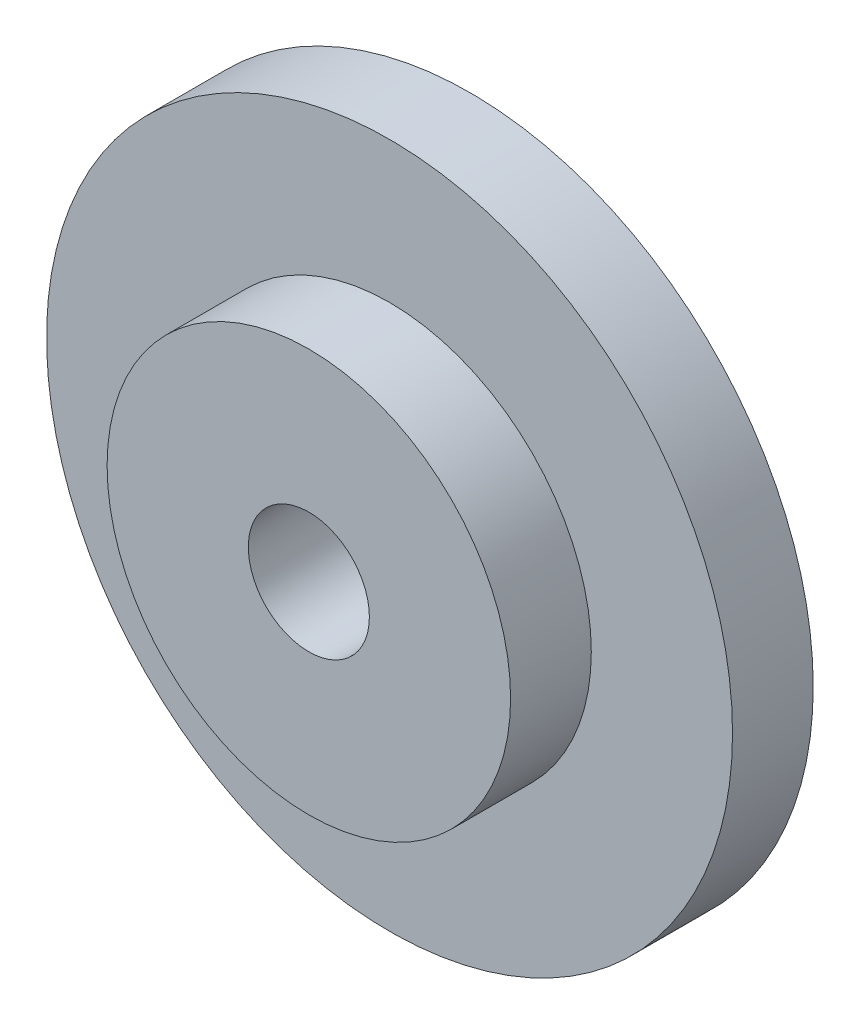
SolidWorks part; units mm, degrees
ref_plane "Front Plane" through (0, 0, 0) normal (0, 0, 1) x (1, 0, 0)
ref_plane "Top Plane" through (0, 0, 0) normal (0, 1, 0) x (1, 0, 0)
ref_plane "Right Plane" through (0, 0, 0) normal (1, 0, 0) x (0, 0, -1)
sketch "Sketch1" plane through (0, 0, 0) normal (0, 0, 1) x (1, 0, 0)
  circle A0 centre (0, 0) radius 8.5
  dimension "D1" = 17
extrude "Boss-Extrude1" add sketch "Sketch1" along normal blind 2
sketch "Sketch2" plane through (0, 0, 2) normal (0, 0, 1) x (1, 0, 0)
  circle A0 centre (0, 0) radius 5
  dimension "D1" = 10
extrude "Boss-Extrude2" add sketch "Sketch2" along normal blind 2
sketch "Sketch3" plane through (0, 0, 4) normal (0, 0, 1) x (1, 0, 0)
  circle A0 centre (0, 0) radius 1.5
extrude "Cut-Extrude1" cut sketch "Sketch3" against normal through all
